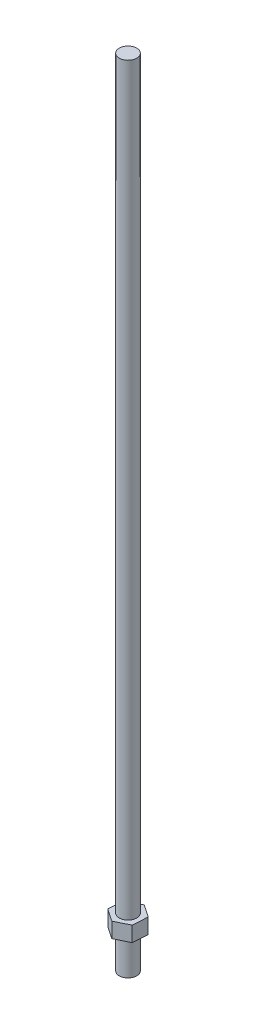
SolidWorks part; units mm, degrees
material "AISI 1010 Steel, hot rolled bar"
ref_plane "Front Plane" through (0, 0, 0) normal (0, 0, 1) x (1, 0, 0)
ref_plane "Top Plane" through (0, 0, 0) normal (0, 1, 0) x (1, 0, 0)
ref_plane "Right Plane" through (0, 0, 0) normal (1, 0, 0) x (0, 0, -1)
sketch "Sketch1" plane through (0, 0, 0) normal (0, 1, 0) x (1, 0, 0)
  circle A0 centre (0, 0) radius 6.35
  dimension "D1" = 12.7
extrude "Boss-Extrude1" add sketch "Sketch1" along normal blind 577.85
sketch "Sketch3" plane through (0, 0, 0) normal (0, 1, 0) x (1, 0, 0)
  line L1 (9.8769, 4.8389) -> (0.7478, 10.9731)
  line L2 (0.7478, 10.9731) -> (-9.129, 6.1342)
  line L3 (-9.129, 6.1342) -> (-9.8769, -4.8389)
  line L4 (-9.8769, -4.8389) -> (-0.7478, -10.9731)
  line L5 (-0.7478, -10.9731) -> (9.129, -6.1342)
  line L6 (9.129, -6.1342) -> (9.8769, 4.8389)
  circle A0 centre (0, 0) radius 9.525 construction
  dimension "D1" = 19.05
extrude "Boss-Extrude2" add sketch "Sketch3" along normal blind 11.049 from offset 25.4
